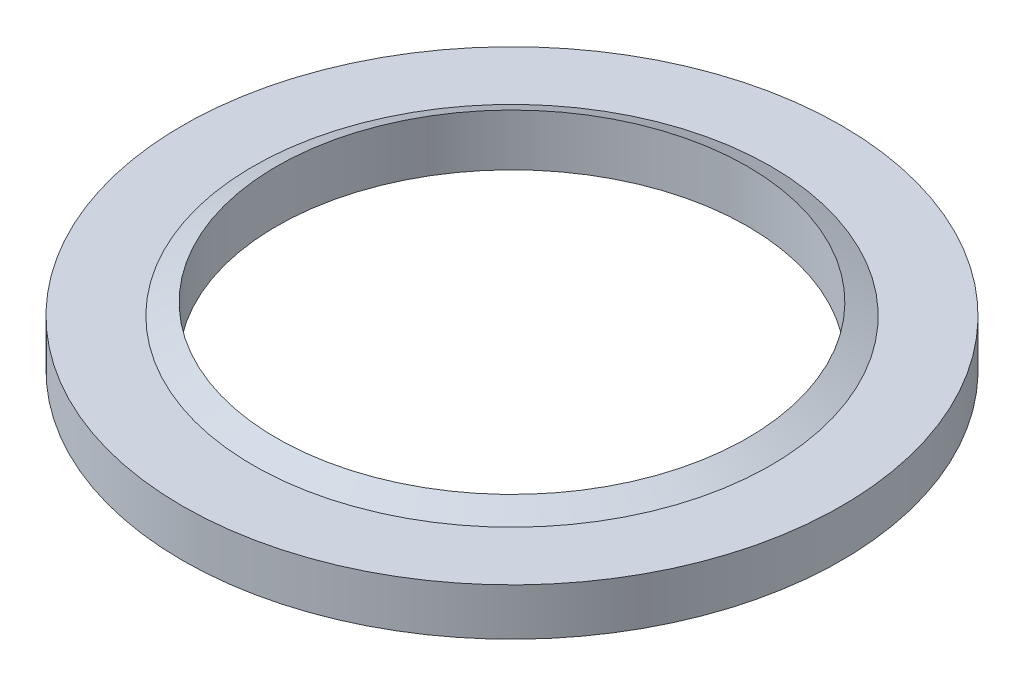
SolidWorks part; units mm, degrees
material "Silicon Rubber"
ref_plane "Front" through (0, 0, 0) normal (0, 0, 1) x (1, 0, 0)
ref_plane "Top" through (0, 0, 0) normal (0, 1, 0) x (1, 0, 0)
ref_plane "Right" through (0, 0, 0) normal (1, 0, 0) x (0, 0, -1)
sketch "Sketch1" plane through (0, 0, 0) normal (0, 0, 1) x (1, 0, 0)
  line L0 (0, 0) -> (0, 35.6954) construction
  line L1 (14, 0) -> (14, 2)
  line L2 (10, 0) -> (10, 2.5)
  line L3 (10, 0) -> (14, 0)
  line L4 (10, 2) -> (14, 2)
  line L7 (10, 2.5) -> (11, 2)
  line L10 (10, 0) -> (10, 35.6954) construction
  line L11 (14, 0) -> (14, 35.6954) construction
  point P10 (14, 2.5)
  point P11 (11, 0)
  point P12 (11, 35.6954)
  dimension "D1" = 14
  dimension "D2" = 4
  dimension "D3" = 2
revolve "Revolve1" add sketch "Sketch1" angle 360 about L0
sketch "Sketch2" plane through (0, 0, 0) normal (0, -1, 0) x (1, 0, 0)
  circle A1 centre (0, 0) radius 10 construction
  circle A2 centre (0, 0) radius 10.5
  circle A3 centre (0, 0) radius 10.5
  circle A4 centre (0, 0) radius 10
  dimension "D1" = 0.5
extrude "Cut-Extrude1" cut sketch "Sketch2" against normal blind 0.3
